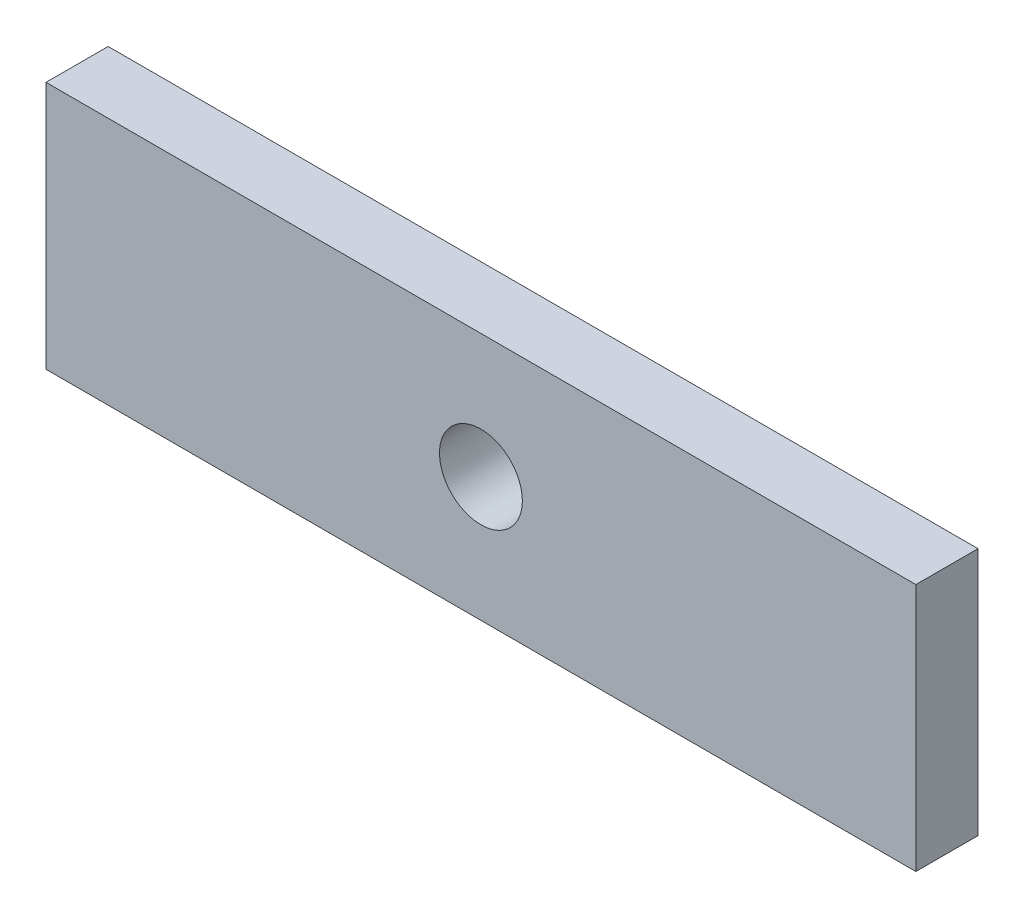
SolidWorks part; units mm, degrees
ref_plane "Front Plane" through (0, 0, 0) normal (0, 0, 1) x (1, 0, 0)
ref_plane "Top Plane" through (0, 0, 0) normal (0, 1, 0) x (1, 0, 0)
ref_plane "Right Plane" through (0, 0, 0) normal (1, 0, 0) x (0, 0, -1)
sketch "Sketch1" plane through (0, 0, 0) normal (0, 0, 1) x (1, 0, 0)
  line L0 (0, 60) -> (420, 60) construction
  line L1 (0, 0) -> (420, 0)
  line L2 (0, 0) -> (0, 120)
  line L3 (0, 120) -> (420, 120)
  line L4 (420, 0) -> (420, 120)
  circle A0 centre (210, 60) radius 20
  dimension "D4" = 40
  dimension "D1" = 210
  dimension "D2" = 210
  dimension "D3" = 120
extrude "Extrude1" add sketch "Sketch1" along normal blind 30
sketch "Sketch3" plane through (0, 0, 0) normal (0, 0, 1) x (1, 0, 0)
  line L0 (-31.7228, 60) -> (443.9766, 60)
  line L1 (0, 0) -> (420, 0) construction
  dimension "D1" = 60
extrude "1/2 Symmetry Model" [suppressed] cut sketch "Sketch3" against normal through all and the other way through all flip side to cut
sketch "Sketch4" plane through (0, 0, 0) normal (0, 0, 1) x (1, 0, 0)
  line L0 (210, 163.1672) -> (210, 11.8084)
  line L1 (0, 120) -> (0, 0) construction
  dimension "D1" = 210
extrude "1/4 Symmetry Model" [suppressed] cut sketch "Sketch4" against normal through all and the other way through all flip side to cut
